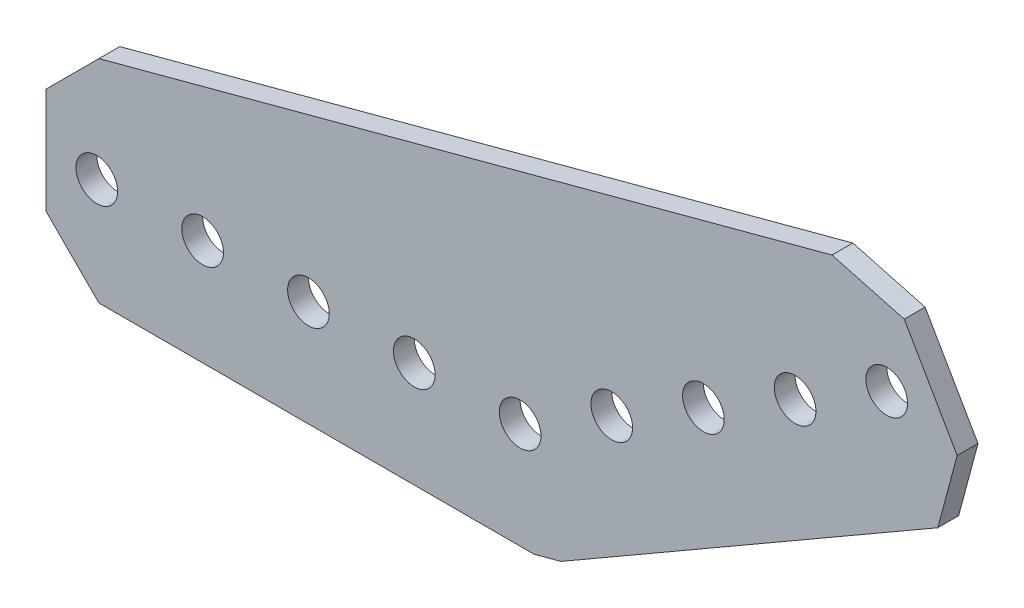
SolidWorks part; units mm, degrees
material "5052-H32"
ref_plane "Front Plane" through (0, 0, 0) normal (0, 0, 1) x (1, 0, 0)
ref_plane "Top Plane" through (0, 0, 0) normal (0, 1, 0) x (1, 0, 0)
ref_plane "Right Plane" through (0, 0, 0) normal (1, 0, 0) x (0, 0, -1)
ref_plane "Plane1" through (0, 0, -1.25) normal (0, 0, -1) x (-1, 0, 0)
sketch "Sketch1" plane through (0, 0, -1.25) normal (0, 0, -1) x (-1, 0, 0)
  line L0 (50.546, 12.7) -> (-37.4241, 36.2715)
  line L1 (-37.4241, 36.2715) -> (-46.0984, 33.9473)
  line L2 (-46.0984, 33.9473) -> (-52.4484, 22.9487)
  line L3 (-52.4484, 22.9487) -> (-50.1241, 14.2745)
  line L4 (-50.1241, 14.2745) -> (-4.902, -11.8345)
  line L5 (-4.902, -11.8345) -> (-1.672, -12.7)
  line L6 (-1.672, -12.7) -> (50.546, -12.7)
  line L7 (50.546, -12.7) -> (56.896, -6.35)
  line L8 (56.896, -6.35) -> (56.896, 6.35)
  line L9 (56.896, 6.35) -> (50.546, 12.7)
  circle A0 centre (12.7, 0) radius 2.5
  circle A1 centre (25.4, 0) radius 2.5
  circle A2 centre (0, 0) radius 2.5
  circle A3 centre (50.8, 0) radius 2.5
  circle A4 centre (38.1, 0) radius 2.5
  circle A5 centre (-43.9941, 25.4) radius 2.5
  circle A6 centre (-32.9956, 19.05) radius 2.5
  circle A7 centre (-21.997, 12.7) radius 2.5
  circle A8 centre (-10.9985, 6.35) radius 2.5
  point P29 (0, 0)
  dimension "D1" = 5
  dimension "D2" = 12.7
  dimension "D3" = 25.4
  dimension "D4" = 38.1
  dimension "D5" = 50.546
  dimension "D6" = 50.8
  dimension "D7" = 56.896
  dimension "D8" = 1.672
  dimension "D9" = 4.902
  dimension "D10" = 10.9985
  dimension "D11" = 21.997
  dimension "D12" = 32.9956
  dimension "D13" = 37.4241
  dimension "D14" = 43.9941
  dimension "D15" = 46.0984
  dimension "D16" = 50.1241
  dimension "D17" = 6.35
  dimension "D18" = 14.2745
  dimension "D20" = 19.05
  dimension "D22" = 25.4
extrude "Boss-Extrude1" add sketch "Sketch1" against normal blind 2.5
